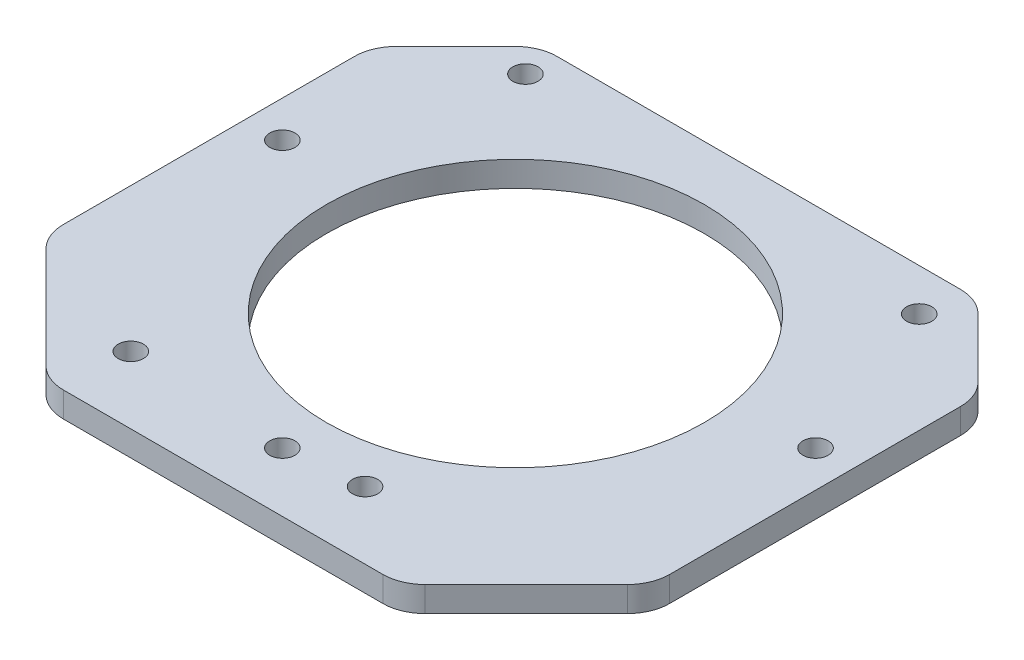
SolidWorks part; units mm, degrees
ref_plane "Front Plane" through (0, 0, 0) normal (0, 0, 1) x (1, 0, 0)
ref_plane "Top Plane" through (0, 0, 0) normal (0, 1, 0) x (1, 0, 0)
ref_plane "Right Plane" through (0, 0, 0) normal (1, 0, 0) x (0, 0, -1)
sketch "Sketch1" plane through (0, 0, 0) normal (0, 1, 0) x (1, 0, 0)
  line L0 (-8.9, -58.8) -> (-8.9, 20.6458) construction
  line L5 (-45, 5) -> (27.2, 5)
  line L6 (-45, 5) -> (-45, -58.8)
  line L7 (-45, -58.8) -> (27.2, -58.8)
  line L8 (27.2, 5) -> (27.2, -58.8)
  line L9 (-40.65, -20) -> (22.85, -20) construction
  circle A0 centre (15.2, 0) radius 1.5
  circle A1 centre (0, -50.8) radius 1.5
  circle A2 centre (-27.9, -50.8) radius 1.5
  circle A3 centre (-33, 1.3) radius 1.5
  circle A4 centre (22.85, -20) radius 1.5
  circle A5 centre (-40.65, -20) radius 1.5
  circle A6 centre (-8.9, -51.75) radius 1.5
  point P0 (0, 0)
  dimension "D1" = 3
  dimension "D7" = 3
  dimension "D8" = 3
  dimension "D11" = 3
  dimension "D16" = 3
  dimension "D17" = 63.5
  dimension "D18" = 20
  dimension "D20" = 3
  dimension "D2" = 15.2
  dimension "D3" = 0
  dimension "D4" = 50.8
  dimension "D5" = 0
  dimension "D6" = 27.9
  dimension "D9" = 1.3
  dimension "D10" = 5.1
  dimension "D12" = 12
  dimension "D13" = 8
  dimension "D14" = 12
  dimension "D15" = 5
  dimension "D19" = 31.75
extrude "Boss-Extrude1" add sketch "Sketch1" along normal mid plane 3
chamfer "Chamfer1" distance 15 angle 45 2 edges at (27.2, 0, 58.8) (-45, 0, 58.8)
chamfer "Chamfer2" distance 10 angle 45 2 edges at (27.2, 0, -5) (-45, 0, -5)
sketch "Sketch2" plane through (0, -1.5, 0) normal (0, -1, 0) x (1, 0, 0)
  line L0 (-8.9, 58.8) -> (-8.9, -5) construction
  line L1 (-30, 58.8) -> (12.2, 58.8) construction
  line L2 (17.2, -5) -> (-35, -5) construction
  circle A0 centre (-8.9, 24) radius 22.5
  point P8 (-8.9, 25.4)
  point P9 (0, 0)
  point P10 (-8.9, 23.5071)
  dimension "D1" = 45
  dimension "D2" = 29
extrude "Cut-Extrude1" cut sketch "Sketch2" against normal through all
fillet "Fillet1" radius 5 8 edges at (27.2, 0, 5) (17.2, 0, -5) (-45, 0, 5) (-35, 0, -5) (27.2, 0, 43.8) (12.2, 0, 58.8) (-45, 0, 43.8) (-30, 0, 58.8)
